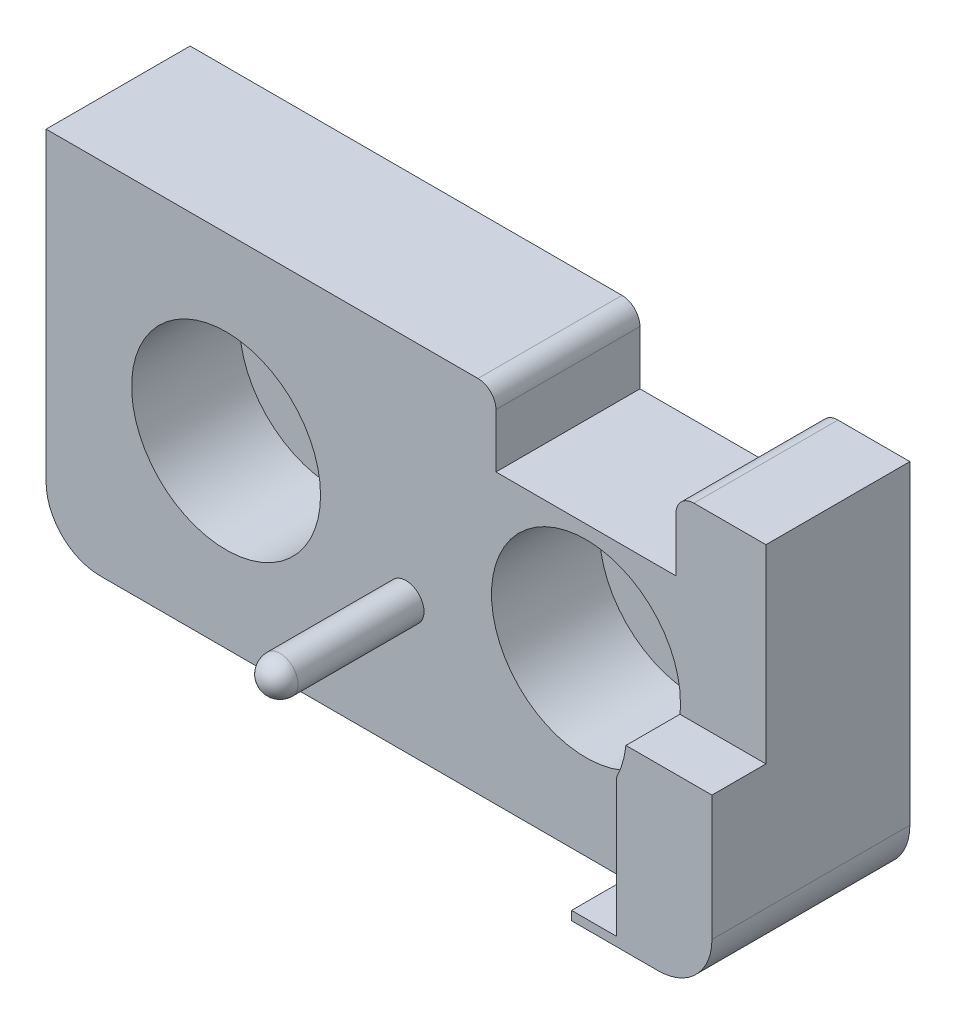
SolidWorks part; units mm, degrees
ref_plane "Front Plane" through (0, 0, 0) normal (0, 0, 1) x (1, 0, 0)
ref_plane "Top Plane" through (0, 0, 0) normal (0, 1, 0) x (1, 0, 0)
ref_plane "Right Plane" through (0, 0, 0) normal (1, 0, 0) x (0, 0, -1)
sketch "Sketch1" plane through (0, 0, 0) normal (0, 0, 1) x (1, 0, 0)
  line L0 (10, 10) -> (10, 6) construction
  line L1 (-17, -10) -> (17, -10)
  line L2 (-20, -7) -> (-20, 10)
  line L3 (-20, 10) -> (4, 10)
  line L4 (20, -7) -> (20, 10)
  line L5 (-20, -10) -> (20, 10) construction
  line L6 (-20, 10) -> (20, -10) construction
  line L8 (5, 9) -> (5, 6)
  line L9 (5, 6) -> (15, 6)
  line L10 (15, 9) -> (15, 6)
  line L11 (-10, 10) -> (-10, -10) construction
  line L12 (10, 6) -> (10, -10) construction
  line L13 (16, 10) -> (20, 10)
  arc A0 (16, 10) -> (15, 9) centre (16, 9) ccw
  arc A1 (4, 10) -> (5, 9) centre (4, 9) cw
  arc A2 (17, -10) -> (20, -7) centre (17, -7) ccw
  arc A3 (-17, -10) -> (-20, -7) centre (-17, -7) cw
  point P0 (0, 0)
  dimension "D7" = 1
  dimension "D8" = 3
  dimension "D1" = 40
  dimension "D2" = 20
  dimension "D3" = 10
  dimension "D4" = 4
  dimension "D5" = 10
  dimension "D6" = 10
extrude "Boss-Extrude1" add sketch "Sketch1" along normal blind 8
hole_wizard "CBORE for M5 SHCS1" positions "Sketch3" profile "Sketch2" counterbore size "M5" standard "ANSI Metric" end condition up to next
sketch "Sketch3" plane through (0, 0, 8) normal (0, 0, 1) x (1, 0, 0)
  line L0 (-10, 10) -> (-10, -10) construction
  line L3 (10, 6) -> (10, -10) construction
  line L4 (-13.9419, 10) -> (-13.9419, -10) construction
  line L5 (-20, 10) -> (4, 10) construction
  line L6 (-17, -10) -> (17, -10) construction
  point P0 (-10, 0)
  point P2 (10, 0)
  point P24 (-13.9419, 0)
sketch "Sketch2" plane through (-10, 0, 8) normal (1, 0, 0) x (0, -1, 0)
  line L0 (0, 0) -> (0, 8)
  line L1 (0, 8) -> (2.75, 8)
  line L3 (2.75, 8) -> (2.75, 6)
  line L4 (2.75, 6) -> (5.25, 6)
  line L5 (5.25, 6) -> (5.25, 0)
  line L7 (5.25, 0) -> (0, 0)
  line L11 (0, -6.35) -> (0, 107.95) construction
  dimension "Thru Hole Dia." = 5.5
  dimension "Thru Hole Depth" = 8
  dimension "C'Bore Dia." = 10.5
  dimension "C'Bore Depth" = 6
sketch "Sketch6" plane through (0, 0, 8) normal (0, 0, 1) x (1, 0, 0)
  line L0 (-20, -2.7273) -> (20, -2.7273) construction
  line L1 (-20, -7) -> (-20, 10) construction
  line L2 (20, -7) -> (20, 10) construction
  line L3 (11.5, -2.7273) -> (-2, -2.7273) construction
  line L4 (0, -10) -> (0, -2.7273) construction
  line L5 (-17, -10) -> (17, -10) construction
  circle A0 centre (0, -2.7273) radius 1
  dimension "D1" = 2
extrude "Boss-Extrude3" add sketch "Sketch6" along normal blind 8
fillet "Fillet2" radius 1 1 edges at (1, -2.7273, 16)
sketch "Sketch7" plane through (0, 0, 8) normal (0, 0, 1) x (1, 0, 0)
  line L0 (20, -7) -> (20, 10) construction
  line L1 (20, -0.55) -> (15.2211, -0.55)
  line L2 (20, -0.55) -> (20, -7.5)
  line L3 (14.5, -1.05) -> (14.5, -9.75) construction
  line L7 (11.5, -0.55) -> (14, -0.55) construction
  line L8 (14.7, -2.3393) -> (14.7, -10)
  line L11 (-17, -10) -> (17, -10) construction
  line L12 (14.7, -10) -> (12.2, -10)
  line L13 (12.2, -10) -> (12.2, -10.5)
  line L14 (12.2, -10.5) -> (17, -10.5)
  arc A0 (20, -7.5) -> (17, -10.5) centre (17, -7.5) cw
  circle A1 centre (10, 0) radius 5.25 construction
  arc A2 (14.7, -2.3393) -> (15.2211, -0.55) centre (10, 0) ccw
  point P6 (14.7, -10)
  dimension "D2" = 0.5
  dimension "D4" = 3
  dimension "D1" = 0.2
  dimension "D3" = 2.5
  dimension "D5" = 5.3
extrude "Boss-Extrude4" add sketch "Sketch7" along normal blind 3 and the other way up to surface (8 mm away) other way up to face at (-7.25, 0, 0)
